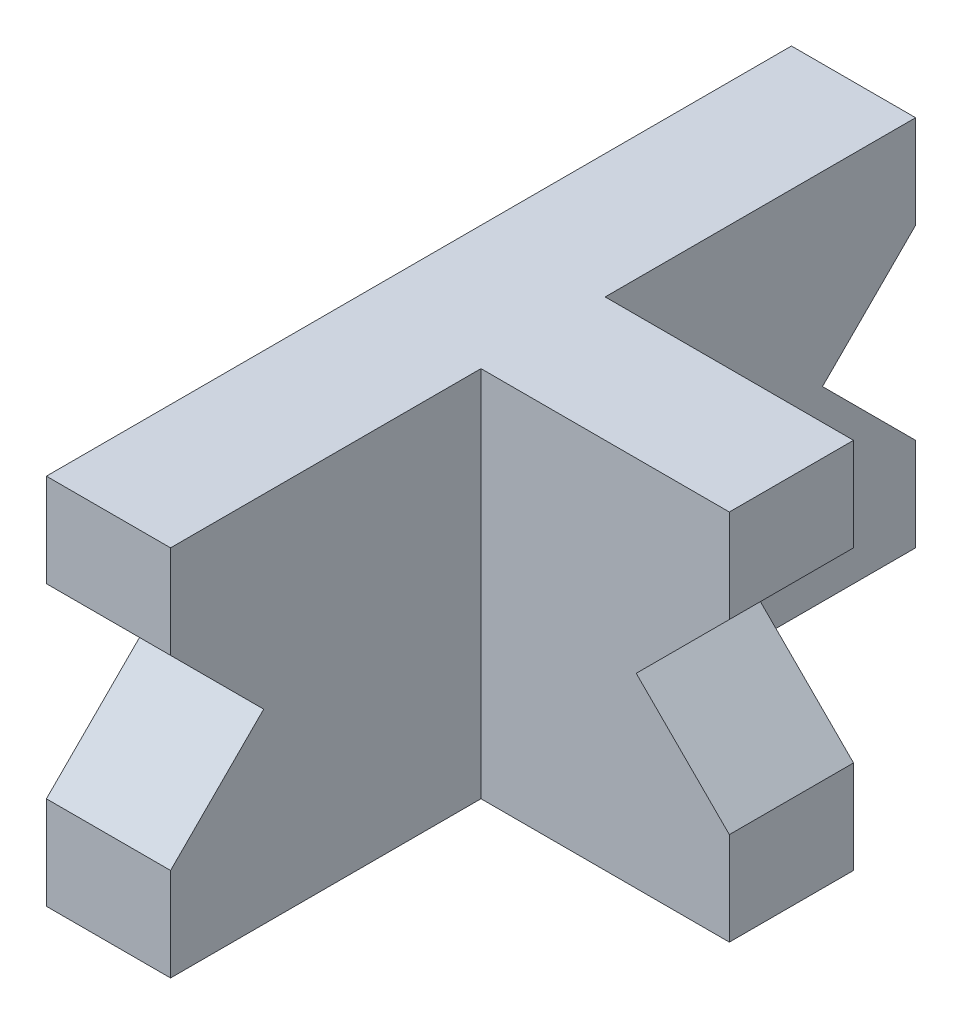
SolidWorks part; units mm, degrees
ref_plane "Front Plane" through (0, 0, 0) normal (0, 0, 1) x (1, 0, 0)
ref_plane "Top Plane" through (0, 0, 0) normal (0, 1, 0) x (1, 0, 0)
ref_plane "Right Plane" through (0, 0, 0) normal (1, 0, 0) x (0, 0, -1)
sketch "Sketch1" plane through (0, 0, 0) normal (1, 0, 0) x (0, 0, -1)
  line L1 (-60, 30) -> (60, 30)
  line L2 (-60, 30) -> (-60, -30)
  line L3 (-60, -30) -> (60, -30)
  line L4 (60, 30) -> (60, -30)
  line L5 (-60, 30) -> (60, -30) construction
  line L6 (-60, -30) -> (60, 30) construction
  point P0 (0, 0)
  dimension "D1" = 120
  dimension "D2" = 60
extrude "Boss-Extrude1" add sketch "Sketch1" along normal blind 20
sketch "Sketch3" plane through (0, 0, 0) normal (-1, 0, 0) x (0, 0, 1)
  line L0 (60, 30) -> (60, 15)
  line L1 (60, 30) -> (60, -30) construction
  line L2 (45, 30) -> (45, -30) construction
  line L3 (-60, 30) -> (60, 30) construction
  line L4 (60, -15) -> (60, -30)
  line L5 (60, -30) -> (-60, -30) construction
  line L6 (60, -15) -> (45, 0)
  line L7 (45, 0) -> (60, 15)
  line L8 (60, 15) -> (60, -15)
  line M10 (60, -30) -> (60, 30)
  dimension "D1" = 15
  dimension "D2" = 15
  dimension "D3" = 90
extrude "Cut-Extrude1" cut sketch "Sketch3" against normal blind 20 contours L7 L6 M10
ref_plane "Plane2" through (0, 0, 0) normal (0, 0, -1) x (-1, 0, 0)
mirror "Mirror4" about plane through (0, 0, 0) normal (0, 0, -1) of "Cut-Extrude1"
sketch "Sketch4" plane through (0, 0, 0) normal (0, 0, 1) x (1, 0, 0)
  line L0 (20, 30) -> (60, 30)
  line L1 (60, 30) -> (60, -30) construction
  line L2 (60, -30) -> (20, -30)
  line L3 (60, 30) -> (60, 15)
  line L4 (60, -30) -> (60, -15)
  line L5 (45, 30) -> (45, -30) construction
  line L6 (60, 15) -> (45, 0)
  line L7 (45, 0) -> (60, -15)
  line L8 (20, 30) -> (20, -30)
  dimension "D1" = 40
  dimension "D2" = 60
  dimension "D3" = 15
  dimension "D4" = 15
  dimension "D5" = 90
extrude "Boss-Extrude2" add sketch "Sketch4" along normal mid plane 20
